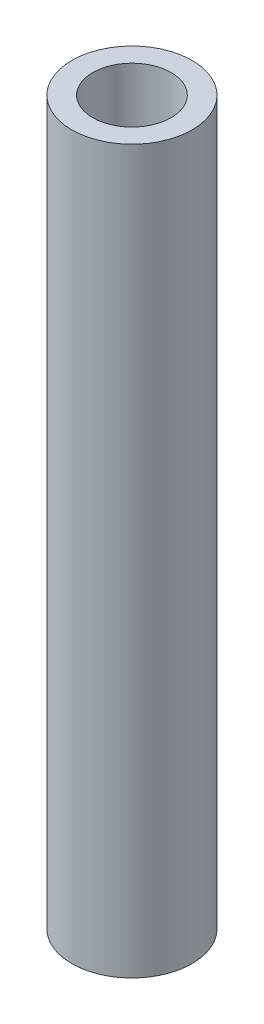
SolidWorks part; units mm, degrees
material "6020 Alloy"
ref_plane "Front Plane" through (0, 0, 0) normal (0, 0, 1) x (1, 0, 0)
ref_plane "Top Plane" through (0, 0, 0) normal (0, 1, 0) x (1, 0, 0)
ref_plane "Right Plane" through (0, 0, 0) normal (1, 0, 0) x (0, 0, -1)
sketch "Sketch1" plane through (0, 0, 0) normal (0, 1, 0) x (1, 0, 0)
  circle A0 centre (0, 0) radius 3.1
  circle A1 centre (0, 0) radius 4.7625
  point P5 (0, 0.3627)
  dimension "D1" = 6.2
  dimension "D2" = 9.525
extrude "Boss-Extrude1" add sketch "Sketch1" along normal blind 57.15 contours A0
